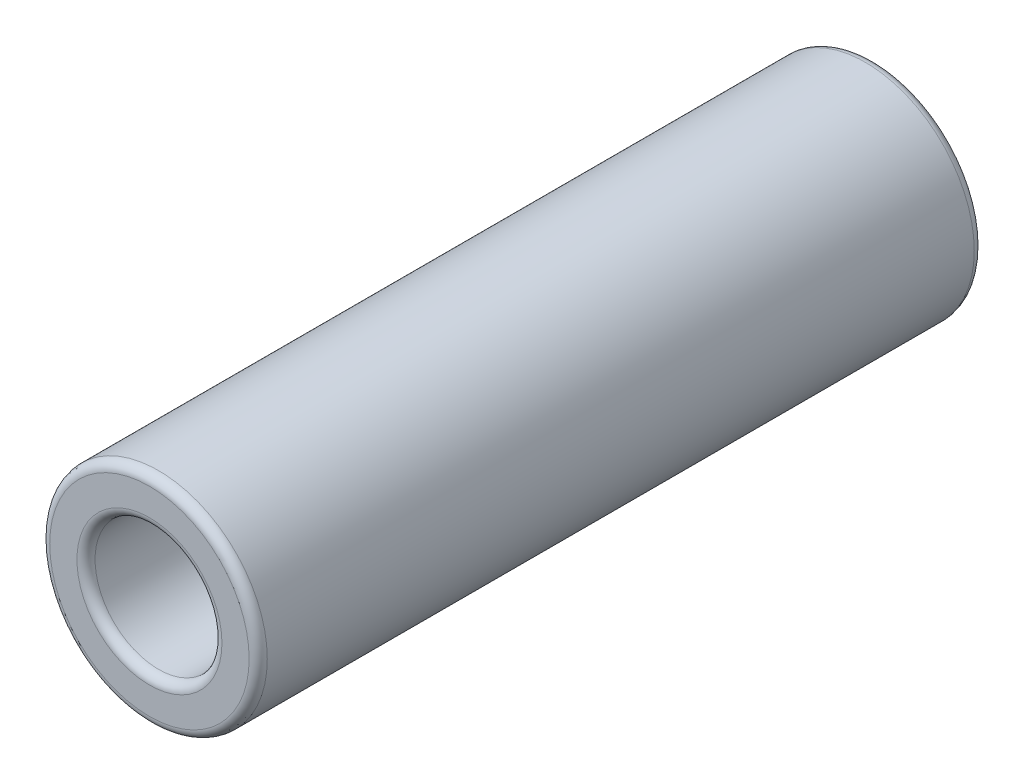
SolidWorks part; units mm, degrees
ref_plane "Front Plane" through (0, 0, 0) normal (0, 0, 1) x (1, 0, 0)
ref_plane "Top Plane" through (0, 0, 0) normal (0, 1, 0) x (1, 0, 0)
ref_plane "Right Plane" through (0, 0, 0) normal (1, 0, 0) x (0, 0, -1)
sketch "Szkic1" plane through (0, 0, 0) normal (0, 0, 1) x (1, 0, 0)
  circle A0 centre (0, 0) radius 6
  circle A1 centre (0, 0) radius 3.5
  dimension "D1" = 12
  dimension "D2" = 7
extrude "Dodanie-wyciągnięcie1" add sketch "Szkic1" along normal blind 40
fillet "Zaokrąglenie1" radius 0.5 4 edges at (3.5, 0, 0) (6, 0, 0) (3.5, 0, 40) (6, 0, 40)
